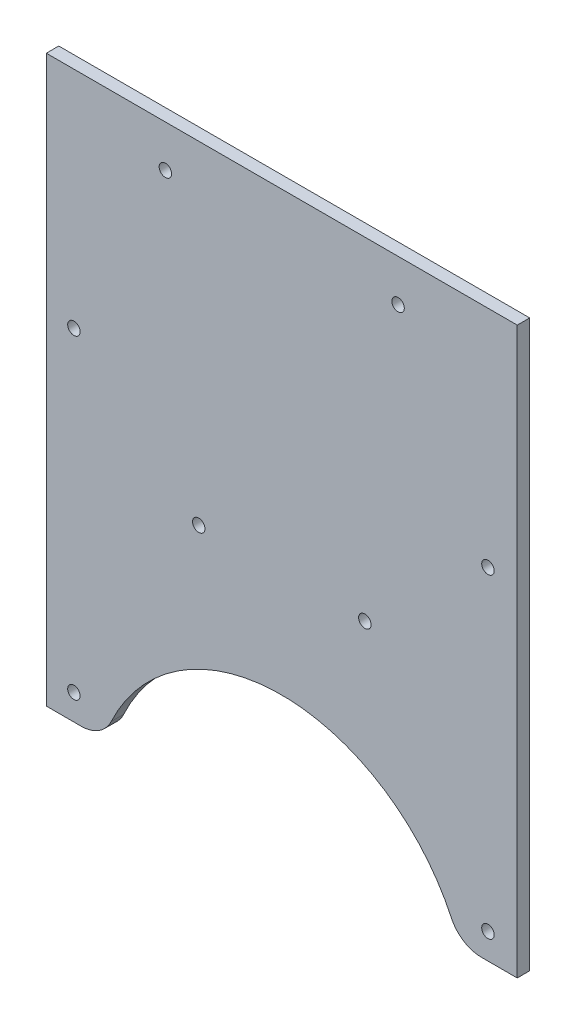
SolidWorks part; units mm, degrees
material "Plastique personnalisé"
ref_plane "Plan de face" through (0, 0, 0) normal (0, 0, 1) x (1, 0, 0)
ref_plane "Plan de dessus" through (0, 0, 0) normal (0, 1, 0) x (1, 0, 0)
ref_plane "Plan de droite" through (0, 0, 0) normal (1, 0, 0) x (0, 0, -1)
sketch "Esquisse1" plane through (0, 0, 0) normal (0, 0, 1) x (1, 0, 0)
  line L1 (0, 0) -> (113.4, 0)
  line L2 (0, 0) -> (0, 180)
  line L3 (0, 180) -> (113.4, 180)
  line L4 (113.4, 0) -> (113.4, 180)
  dimension "D1" = 113.4
  dimension "D2" = 180
extrude "Boss.-Extru.1" add sketch "Esquisse1" along normal blind 3
sketch "Esquisse2" plane through (0, 0, 3) normal (0, 0, 1) x (1, 0, 0)
  circle A0 centre (106.3466, 50.0375) radius 1.5
  circle A1 centre (6.6474, 50.0375) radius 1.5
  circle A2 centre (6.6474, 125.9625) radius 1.5
  circle A3 centre (106.3466, 125.9625) radius 1.5
extrude "Enlèv. mat.-Extru.1" cut sketch "Esquisse2" against normal blind 10
sketch "Esquisse3" plane through (0, 0, 3) normal (0, 0, 1) x (1, 0, 0)
  circle A0 centre (76.7062, 99.9164) radius 1.5
  circle A1 centre (36.7062, 99.9164) radius 1.5
  circle A2 centre (84.7062, 169.9164) radius 1.5
  circle A3 centre (28.6759, 169.9164) radius 1.5
extrude "Enlèv. mat.-Extru.2" cut sketch "Esquisse3" against normal blind 10
sketch "Esquisse5" plane through (0, 0, 3) normal (0, 0, 1) x (1, 0, 0)
  line L0 (113.4, 0) -> (113.4, 180) construction
  line L1 (113.4, 43.8463) -> (-0.6904, 43.8463)
  line L2 (113.4, 43.8463) -> (113.4, -1.3064)
  line L3 (113.4, -1.3064) -> (-0.6904, -1.3064)
  line L4 (-0.6904, 43.8463) -> (-0.6904, -1.3064)
  point P6 (113.4, -1.3064)
extrude "Enlèv. mat.-Extru.3" cut sketch "Esquisse5" against normal blind 10
sketch "Esquisse6" plane through (0, 0, 3) normal (0, 0, 1) x (1, 0, 0)
  line L0 (113.4, 43.8463) -> (99.3944, 43.8463) construction
  line L1 (113.4, 43.8463) -> (0, 43.8463) construction
  line L2 (99.3944, 4) -> (99.3944, 180) construction
  line L3 (0, 43.8463) -> (13.7802, 43.8463) construction
  line L4 (13.7802, 180) -> (13.7802, 4) construction
  line L5 (99.3944, 43.8463) -> (13.7802, 43.8463)
  arc A0 (99.3944, 43.8463) -> (13.7802, 43.8463) centre (56.5873, 29.2939) ccw
extrude "Enlèv. mat.-Extru.4" cut sketch "Esquisse6" against normal blind 10
fillet "Congé2" radius 8 2 edges at (99.3944, 43.8463, 1.5) (13.7802, 43.8463, 1.5)
